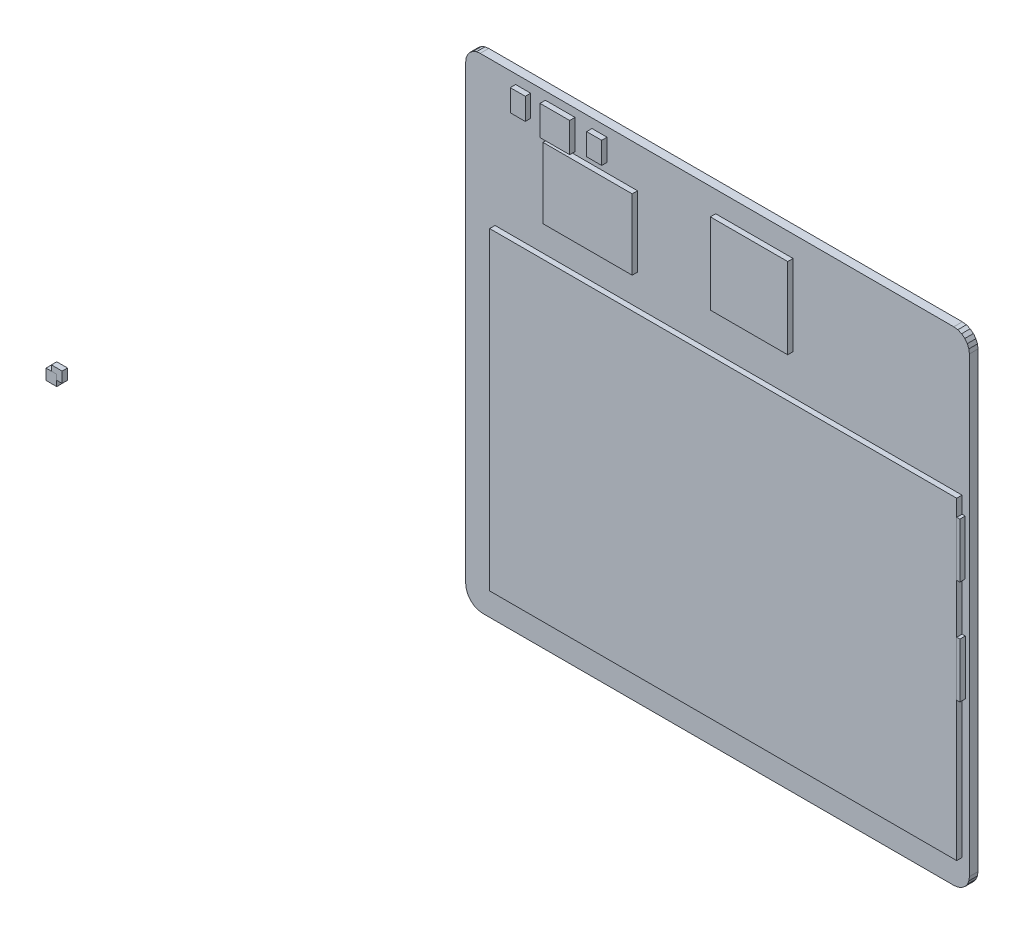
SolidWorks part; units mm, degrees
ref_plane "Plan de face" through (0, 0, 0) normal (0, 0, 1) x (1, 0, 0)
ref_plane "Plan de dessus" through (0, 0, 0) normal (0, 1, 0) x (1, 0, 0)
ref_plane "Plan de droite" through (0, 0, 0) normal (1, 0, 0) x (0, 0, -1)
sketch "Esquisse1" plane through (0, 0, 0) normal (0, 0, 1) x (1, 0, 0)
  line L0 (0, 87.476) -> (0, 3.1945)
  line L1 (0, 3.1945) -> (0.1089, 2.3677)
  line L2 (0.1089, 2.3677) -> (0.428, 1.5973)
  line L3 (0.428, 1.5973) -> (0.9357, 0.9357)
  line L4 (0.9357, 0.9357) -> (1.5973, 0.428)
  line L5 (1.5973, 0.428) -> (2.3677, 0.1089)
  line L6 (2.3677, 0.1089) -> (3.1945, 0)
  line L7 (3.1945, 0) -> (91.0111, 0)
  line L8 (91.0111, 0) -> (91.7562, 0.0981)
  line L9 (91.7562, 0.0981) -> (92.4505, 0.3857)
  line L10 (92.4505, 0.3857) -> (93.0468, 0.8432)
  line L11 (93.0468, 0.8432) -> (93.5043, 1.4395)
  line L12 (93.5043, 1.4395) -> (93.7919, 2.1338)
  line L13 (93.7919, 2.1338) -> (93.89, 2.8789)
  line L14 (93.89, 2.8789) -> (93.89, 87.2525)
  line L15 (93.89, 87.2525) -> (93.7906, 88.0076)
  line L16 (93.7906, 88.0076) -> (93.4991, 88.7113)
  line L17 (93.4991, 88.7113) -> (93.0355, 89.3155)
  line L18 (93.0355, 89.3155) -> (92.4313, 89.7791)
  line L19 (92.4313, 89.7791) -> (91.7276, 90.0706)
  line L20 (91.7276, 90.0706) -> (90.9725, 90.17)
  line L21 (90.9725, 90.17) -> (2.694, 90.17)
  line L22 (2.694, 90.17) -> (1.9967, 90.0782)
  line L23 (1.9967, 90.0782) -> (1.347, 89.8091)
  line L24 (1.347, 89.8091) -> (0.7891, 89.3809)
  line L25 (0.7891, 89.3809) -> (0.3609, 88.823)
  line L26 (0.3609, 88.823) -> (0.0918, 88.1733)
  line L27 (0.0918, 88.1733) -> (0, 87.476)
extrude "BOARD" add sketch "Esquisse1" along normal blind 1.6 separate body
ref_plane "Plan1" through (0, 0, 1.6) normal (0, 0, 1) x (1, 0, 0)
sketch "Esquisse2" plane through (0, 0, 1.6) normal (0, 0, 1) x (1, 0, 0)
  line L0 (23.0396, 39.5262) -> (23.0396, 42.523)
  line L1 (23.0396, 42.523) -> (25.031, 42.523)
  line L2 (25.031, 42.523) -> (25.031, 39.5262)
  line L3 (25.031, 39.5262) -> (23.0396, 39.5262)
extrude "0603-CAP-1" add sketch "Esquisse2" along normal blind 1 separate body
sketch "Esquisse3" plane through (0, 0, 1.6) normal (0, 0, 1) x (1, 0, 0)
  line L0 (22.4056, 36.8088) -> (19.4088, 36.8088)
  line L1 (19.4088, 36.8088) -> (19.4088, 38.8002)
  line L2 (19.4088, 38.8002) -> (22.4056, 38.8002)
  line L3 (22.4056, 38.8002) -> (22.4056, 36.8088)
extrude "0603-CAP-2" add sketch "Esquisse3" along normal blind 1 separate body
sketch "Esquisse4" plane through (0, 0, 1.6) normal (0, 0, 1) x (1, 0, 0)
  line L0 (25.486, 36.8134) -> (22.4892, 36.8134)
  line L1 (22.4892, 36.8134) -> (22.4892, 38.8048)
  line L2 (22.4892, 38.8048) -> (25.486, 38.8048)
  line L3 (25.486, 38.8048) -> (25.486, 36.8134)
extrude "0603-CAP-3" add sketch "Esquisse4" along normal blind 1 separate body
sketch "Esquisse5" plane through (0, 0, 1.6) normal (0, 0, 1) x (1, 0, 0)
  line L0 (27.8414, 28.8464) -> (30.8382, 28.8464)
  line L1 (30.8382, 28.8464) -> (30.8382, 26.855)
  line L2 (30.8382, 26.855) -> (27.8414, 26.855)
  line L3 (27.8414, 26.855) -> (27.8414, 28.8464)
extrude "0603-CAP-4" add sketch "Esquisse5" along normal blind 1 separate body
sketch "Esquisse6" plane through (0, 0, 1.6) normal (0, 0, 1) x (1, 0, 0)
  line L0 (-74.23, -1.08) -> (-76.23, -1.08)
  line L1 (-76.23, -1.08) -> (-76.23, 0.92)
  line L2 (-76.23, 0.92) -> (-74.23, 0.92)
  line L3 (-74.23, 0.92) -> (-74.23, -1.08)
extrude "DUMMY-1" add sketch "Esquisse6" along normal blind 1 separate body
sketch "Esquisse7" plane through (0, 0, 1.6) normal (0, 0, 1) x (1, 0, 0)
  line L0 (-75.24, -2.1) -> (-77.24, -2.1)
  line L1 (-77.24, -2.1) -> (-77.24, -0.1)
  line L2 (-77.24, -0.1) -> (-75.24, -0.1)
  line L3 (-75.24, -0.1) -> (-75.24, -2.1)
extrude "DUMMY-2" add sketch "Esquisse7" along normal blind 1 separate body
sketch "Esquisse8" plane through (0, 0, 1.6) normal (0, 0, 1) x (1, 0, 0)
  line L0 (26.34, 84.3965) -> (23.54, 84.3965)
  line L1 (23.54, 84.3965) -> (23.54, 88.46)
  line L2 (23.54, 88.46) -> (26.34, 88.46)
  line L3 (26.34, 88.46) -> (26.34, 84.3965)
extrude "U_FL-1" add sketch "Esquisse8" along normal blind 1 separate body
sketch "Esquisse9" plane through (0, 0, 1.6) normal (0, 0, 1) x (1, 0, 0)
  line L0 (9.3, 88.4435) -> (12.1, 88.4435)
  line L1 (12.1, 88.4435) -> (12.1, 84.38)
  line L2 (12.1, 84.38) -> (9.3, 84.38)
  line L3 (9.3, 84.38) -> (9.3, 88.4435)
extrude "U_FL-2" add sketch "Esquisse9" along normal blind 1 separate body
sketch "Esquisse10" plane through (0, 0, 1.6) normal (0, 0, 1) x (1, 0, 0)
  line L0 (90.4584, 50.52) -> (90.4584, 60.68)
  line L1 (90.4584, 60.68) -> (93.1, 60.68)
  line L2 (93.1, 60.68) -> (93.1, 50.52)
  line L3 (93.1, 50.52) -> (90.4584, 50.52)
extrude "1X04-1" add sketch "Esquisse10" along normal blind 1 separate body
sketch "Esquisse11" plane through (0, 0, 1.6) normal (0, 0, 1) x (1, 0, 0)
  line L0 (90.4748, 31.1658) -> (90.4748, 41.3258)
  line L1 (90.4748, 41.3258) -> (93.1164, 41.3258)
  line L2 (93.1164, 41.3258) -> (93.1164, 31.1658)
  line L3 (93.1164, 31.1658) -> (90.4748, 31.1658)
extrude "1X04-2" add sketch "Esquisse11" along normal blind 1 separate body
sketch "2X3-1 [0]" plane through (0, 0, 1.6) normal (0, 0, 1) x (1, 0, 0)
  line L0 (33.8074, 88.519) -> (41.529, 88.519)
  line L1 (41.529, 88.519) -> (41.529, 83.104)
  line L2 (41.529, 83.104) -> (33.8074, 83.104)
  line L3 (33.8074, 83.104) -> (33.8074, 88.519)
sketch "2X3-2 [0]" plane through (0, 0, 1.6) normal (0, 0, 1) x (1, 0, 0)
  line L0 (43.5166, 76.3924) -> (43.5166, 68.6708)
  line L1 (43.5166, 68.6708) -> (38.1016, 68.6708)
  line L2 (38.1016, 68.6708) -> (38.1016, 76.3924)
  line L3 (38.1016, 76.3924) -> (43.5166, 76.3924)
sketch "Esquisse14" plane through (0, 0, 1.6) normal (0, 0, 1) x (1, 0, 0)
  line L0 (5.4565, 63.77) -> (92.52, 63.77)
  line L1 (92.52, 63.77) -> (92.52, 5.27)
  line L2 (92.52, 5.27) -> (5.4565, 5.27)
  line L3 (5.4565, 5.27) -> (5.4565, 63.77)
extrude "RPI3-1" add sketch "Esquisse14" along normal blind 1 separate body
sketch "Esquisse15" plane through (0, 0, 1.6) normal (0, 0, 1) x (1, 0, 0)
  line L0 (29.3723, 29.1645) -> (18.7484, 29.1645)
  line L1 (18.7484, 29.1645) -> (18.7484, 35.832)
  line L2 (18.7484, 35.832) -> (29.3723, 35.832)
  line L3 (29.3723, 35.832) -> (29.3723, 29.1645)
extrude "SO016-1" add sketch "Esquisse15" along normal blind 1 separate body
sketch "Esquisse16" plane through (0, 0, 1.6) normal (0, 0, 1) x (1, 0, 0)
  line L0 (14.8468, 83.1468) -> (14.8468, 88.677)
  line L1 (14.8468, 88.677) -> (20.377, 88.677)
  line L2 (20.377, 88.677) -> (20.377, 83.1468)
  line L3 (20.377, 83.1468) -> (14.8468, 83.1468)
extrude "QFN32-5X5MM-1" add sketch "Esquisse16" along normal blind 1 separate body
sketch "Esquisse17" plane through (0, 0, 1.6) normal (0, 0, 1) x (1, 0, 0)
  line L0 (15.4, 69.5238) -> (15.4, 82.6556)
  line L1 (15.4, 82.6556) -> (32.0256, 82.6556)
  line L2 (32.0256, 82.6556) -> (32.0256, 69.5238)
  line L3 (32.0256, 69.5238) -> (15.4, 69.5238)
extrude "S1216_24PIN_PACKAGE-1" add sketch "Esquisse17" along normal blind 1 separate body
sketch "Esquisse18" plane through (0, 0, 1.6) normal (0, 0, 1) x (1, 0, 0)
  line L0 (46.5914, 71.1734) -> (46.5914, 86.2274)
  line L1 (46.5914, 86.2274) -> (61.0184, 86.2274)
  line L2 (61.0184, 86.2274) -> (61.0184, 71.1734)
  line L3 (61.0184, 71.1734) -> (46.5914, 71.1734)
extrude "PN87520-1" add sketch "Esquisse18" along normal blind 1 separate body
sketch "Esquisse19" plane through (0, 0, 1.6) normal (0, 0, 1) x (1, 0, 0)
  line L0 (22.6835, 39.6607) -> (19.42, 39.6607)
  line L1 (19.42, 39.6607) -> (19.42, 42.2877)
  line L2 (19.42, 42.2877) -> (22.6835, 42.2877)
  line L3 (22.6835, 42.2877) -> (22.6835, 39.6607)
extrude "CRYSTAL-SMD-3_2X2_5-1" add sketch "Esquisse19" along normal blind 1 separate body
